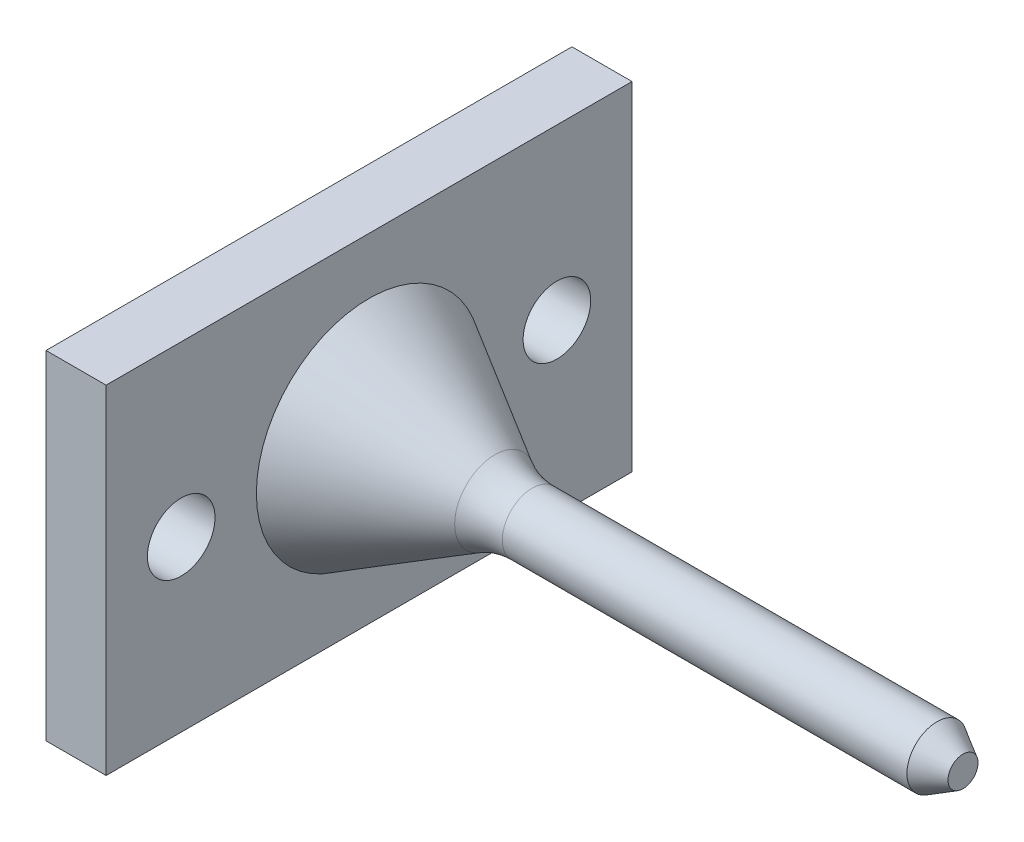
SolidWorks part; units mm, degrees
ref_plane "Ebene vorne" through (0, 0, 0) normal (0, 0, 1) x (1, 0, 0)
ref_plane "Ebene oben" through (0, 0, 0) normal (0, 1, 0) x (1, 0, 0)
ref_plane "Ebene rechts" through (0, 0, 0) normal (1, 0, 0) x (0, 0, -1)
sketch "Skizze1" plane through (0, 0, 0) normal (0, 0, 1) x (1, 0, 0)
  line L0 (0, 0) -> (129.3247, 0) construction
  line L1 (79.0526, 0) -> (79.0526, 4)
  line L2 (79.0526, 4) -> (21.7321, 4)
  line L3 (16.7321, 5.3397) -> (0, 15)
  line L4 (0, 15) -> (0, 0)
  line L5 (0, 0) -> (79.0526, 0)
  arc A0 (21.7321, 4) -> (16.7321, 5.3397) centre (21.7321, 14) cw
  point P9 (19.0526, 4)
  dimension "D6" = 10
  dimension "D1" = 60
  dimension "D2" = 4
  dimension "D3" = 79.0526
  dimension "D4" = 15
  dimension "D5" = 60
revolve "Rotation1" add sketch "Skizze1" angle 360 about L0
chamfer "Fase1" distance 2 angle 60 1 edges at (79.0526, 0, 4)
sketch "Skizze2" plane through (0, 0, 0) normal (-1, 0, 0) x (0, 0, 1)
  line L0 (-35, 0) -> (35, 0) construction
  line L1 (-35, 22.5) -> (35, 22.5)
  line L2 (-35, 22.5) -> (-35, -22.5)
  line L3 (-35, -22.5) -> (35, -22.5)
  line L4 (35, 22.5) -> (35, -22.5)
  circle A1 centre (-25, 0) radius 4.5
  circle A2 centre (25, 0) radius 4.5
  dimension "D3" = 9
  dimension "D1" = 45
  dimension "D2" = 70
  dimension "D4" = 50
  dimension "D5" = 10
extrude "Aufsatz-Linear austragen1" add sketch "Skizze2" along normal blind 8
